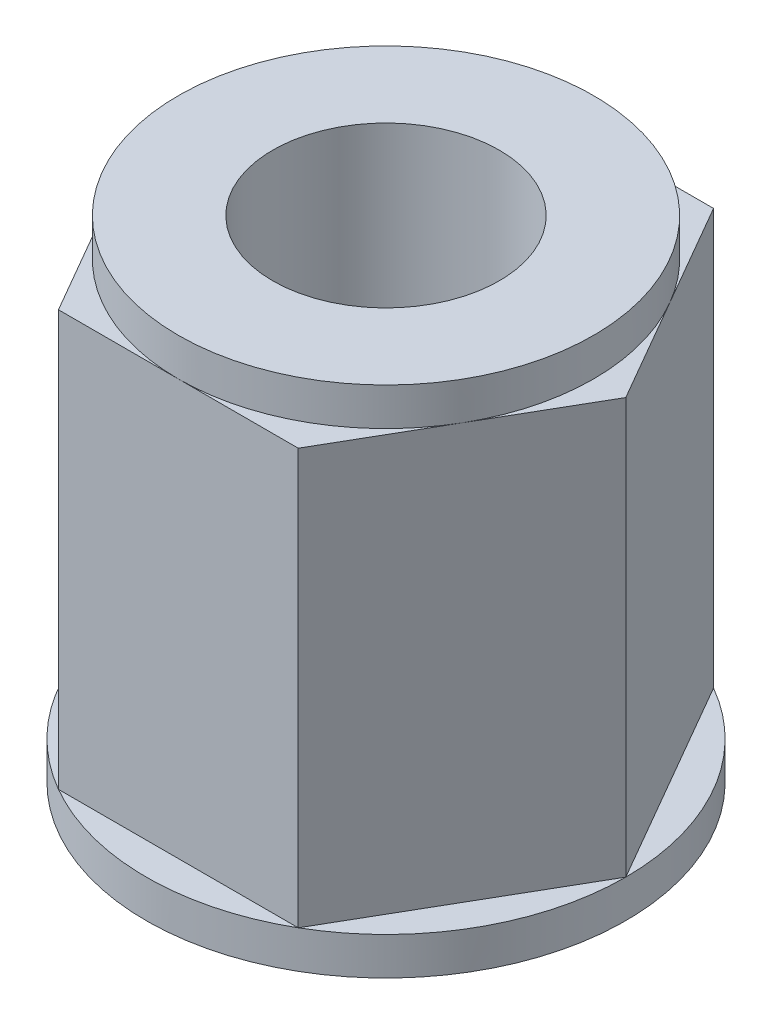
SolidWorks part; units mm, degrees
material "Acciaio in lega"
ref_plane "Piano frontale" through (0, 0, 0) normal (0, 0, 1) x (1, 0, 0)
ref_plane "Piano superiore" through (0, 0, 0) normal (0, 1, 0) x (1, 0, 0)
ref_plane "Piano destro" through (0, 0, 0) normal (1, 0, 0) x (0, 0, -1)
ref_plane "Piano1" through (0, 11, 0) normal (0, 1, 0) x (1, 0, 0)
sketch "Schizzo1" plane through (0, 11, 0) normal (0, 1, 0) x (1, 0, 0)
  line L0 (-3.175, 5.4993) -> (-6.35, 0)
  line L1 (-6.35, 0) -> (-3.175, -5.4993)
  line L2 (-3.175, -5.4993) -> (3.175, -5.4993)
  line L3 (3.175, -5.4993) -> (6.35, 0)
  line L4 (6.35, 0) -> (3.175, 5.4993)
  line L5 (3.175, 5.4993) -> (-3.175, 5.4993)
extrude "Estrusione-Estrusione1" add sketch "Schizzo1" against normal blind 11
sketch "Schizzo2" plane through (0, 0, 0) normal (0, -1, 0) x (1, 0, 0)
  circle A0 centre (0, 0) radius 6.35
extrude "Estrusione-Estrusione2" add sketch "Schizzo2" along normal blind 1
sketch "Schizzo3" plane through (0, 11, 0) normal (0, 1, 0) x (-1, 0, 0)
  circle A0 centre (0, 0) radius 5.4993
extrude "Estrusione-Estrusione3" add sketch "Schizzo3" along normal blind 1
hole_wizard "Foro Ø0.6 (0.6)-1" positions "Schizzo5" profile "Schizzo4" hole size "Ø0.6" standard "Ansi Metric"
sketch "Schizzo5" plane through (0, -1, 0) normal (0, -1, 0) x (-1, 0, 0)
  point P0 (0, 0)
sketch "Schizzo4" plane through (0, -1, 0) normal (1, 0, 0) x (0, 0, -1)
  line L0 (0, 0) -> (0, 13)
  line L1 (0, 13) -> (3, 13)
  line L2 (3, 13) -> (3, 0)
  line L5 (3, 0) -> (0, 0)
  line L11 (0, -6.35) -> (0, 107.95) construction
  dimension "Thru Hole Dia." = 6
  dimension "Thru Hole Depth" = 13
